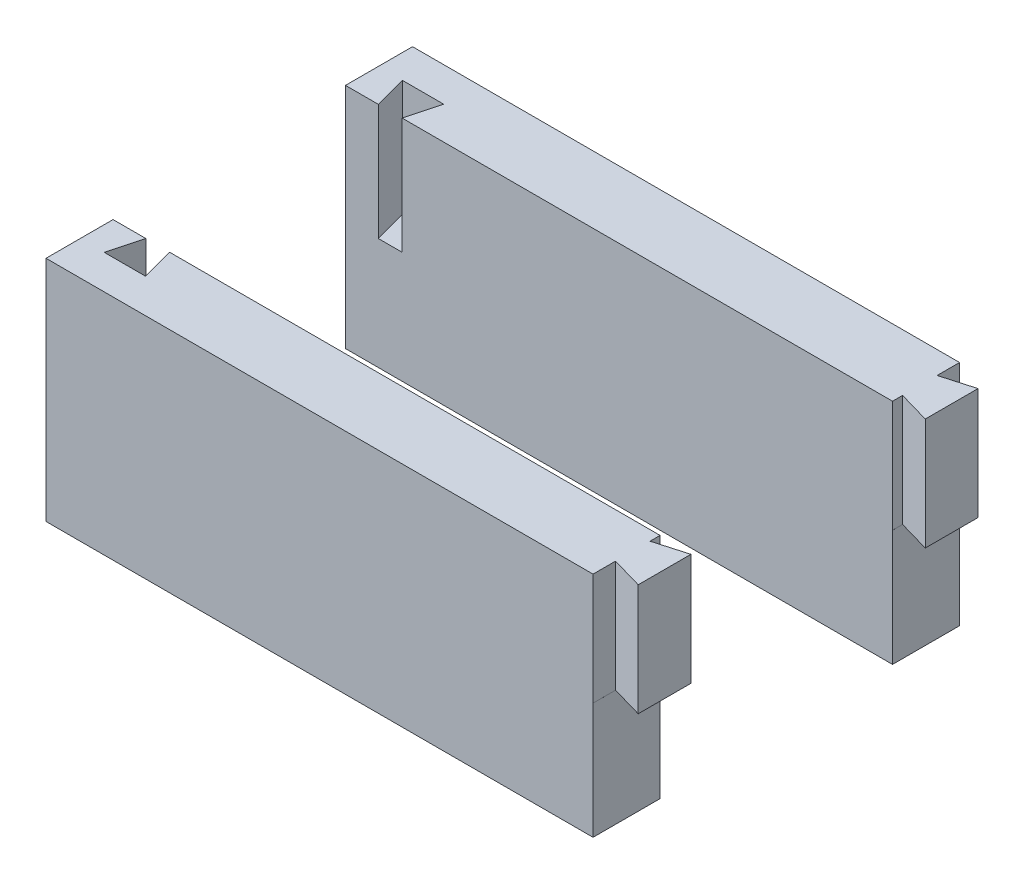
SolidWorks part; units mm, degrees
ref_plane "Front Plane" through (0, 0, 0) normal (0, 0, 1) x (1, 0, 0)
ref_plane "Top Plane" through (0, 0, 0) normal (0, 1, 0) x (1, 0, 0)
ref_plane "Right Plane" through (0, 0, 0) normal (1, 0, 0) x (0, 0, -1)
sketch "Sketch1" plane through (0, 0, 0) normal (0, 0, 1) x (1, 0, 0)
  line L1 (-60.9366, 28.6127) -> (68.5634, 28.6127)
  line L2 (-60.9366, 28.6127) -> (-60.9366, -22.3873)
  line L3 (-60.9366, -22.3873) -> (68.5634, -22.3873)
  line L4 (68.5634, 28.6127) -> (68.5634, -22.3873)
  dimension "D1" = 51
  dimension "D2" = 129.5
extrude "Boss-Extrude1" add sketch "Sketch1" along normal blind 15
sketch "Sketch3" plane through (0, 28.6127, 0) normal (0, 1, 0) x (1, 0, 0)
  line L0 (-60.9366, 0) -> (-53.5866, 0)
  line L2 (68.5634, 0) -> (-60.9366, 0) construction
  line L3 (-53.5866, 0) -> (-55.5536, -7.341)
  line L4 (-55.5536, -7.341) -> (-46.3196, -7.341)
  line L5 (-46.3196, -7.341) -> (-48.2866, 0)
  dimension "D1" = 7.35
  dimension "D2" = 105
  dimension "D3" = 105
  dimension "D4" = 75
  dimension "D5" = 75
  dimension "D6" = 7.6
  dimension "D7" = 7.6
  dimension "D8" = 5.3
  dimension "D9" = 9.234
extrude "Cut-Extrude2" cut sketch "Sketch3" against normal blind 26 and the other way through all
sketch "Sketch5" plane through (0, 28.6127, 0) normal (0, 1, 0) x (1, 0, 0)
  line L3 (61.45, 0) -> (68.5634, 0)
  line L4 (68.5634, 0) -> (-48.2866, 0) construction
  line L5 (68.5634, 0) -> (68.5634, -0.2103)
  line L6 (68.5634, -15) -> (68.5634, 0) construction
  line L7 (68.5634, -0.2103) -> (61.45, -2.25)
  line L8 (61.45, -2.25) -> (61.45, 0)
  line L9 (61.45, -15) -> (61.45, -9.9706)
  line L10 (68.5634, -15) -> (-60.9366, -15) construction
  line L11 (61.45, -9.9706) -> (68.5634, -12.0103)
  line L12 (68.5634, -12.0103) -> (68.5634, -15)
  line L13 (68.5634, -15) -> (61.45, -15)
  dimension "D1" = 7.4
  dimension "D2" = 7.4
  dimension "D3" = 106
  dimension "D4" = 7.1133
  dimension "D5" = 11.8
  dimension "D6" = 2.25
extrude "Cut-Extrude4" cut sketch "Sketch5" against normal blind 25
sketch "Sketch7" plane through (0, -22.3873, 0) normal (0, -1, 0) x (1, 0, 0)
  line L0 (-60.9366, 0) -> (68.5634, 0) construction
  line L1 (61.4534, 0) -> (68.5634, 0)
  line L2 (61.4534, 0) -> (61.4534, 15)
  line L3 (61.4534, 15) -> (68.5634, 15)
  line L4 (68.5634, 0) -> (68.5634, 15)
  dimension "D1" = 7.11
extrude "Cut-Extrude5" cut sketch "Sketch7" against normal blind 26
ref_plane "Plane3" through (0, 0, -26) normal (0, 0, -1) x (-1, 0, 0)
mirror "Mirror2" about plane through (0, 0, -26) normal (0, 0, -1) of bodies 107
